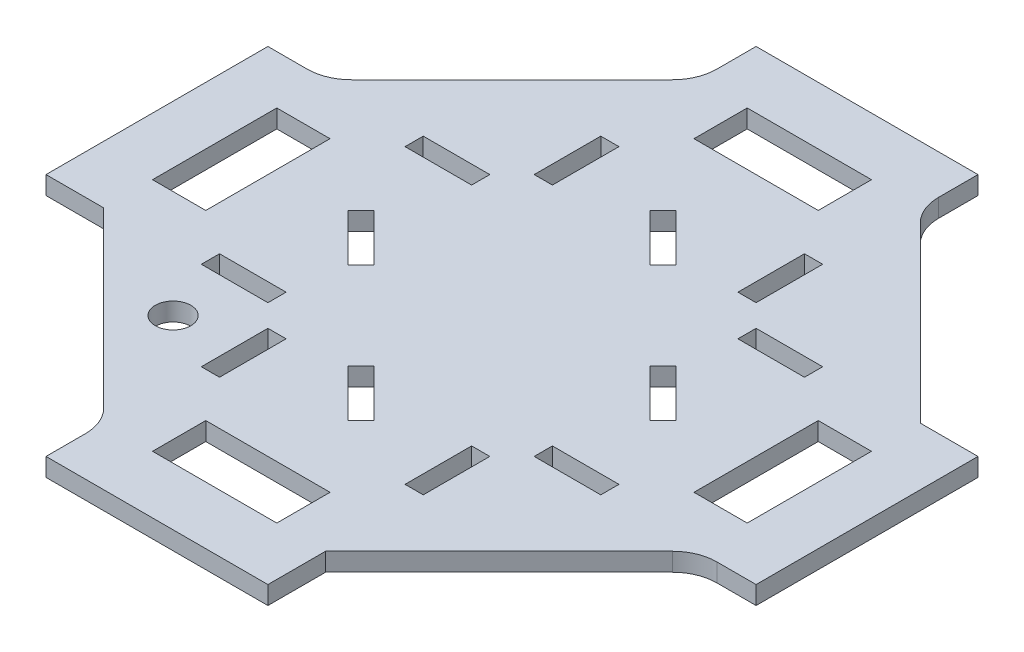
SolidWorks part; units mm, degrees
material "Corrugated Paper"
ref_plane "Front Plane" through (0, 0, 0) normal (0, 0, 1) x (1, 0, 0)
ref_plane "Top Plane" through (0, 0, 0) normal (0, 1, 0) x (1, 0, 0)
ref_plane "Right Plane" through (0, 0, 0) normal (1, 0, 0) x (0, 0, -1)
sketch "Sketch1" plane through (0, 0, 0) normal (0, 1, 0) x (1, 0, 0)
  line L0 (-20.9, 30) -> (-25, 30)
  line L1 (-55, -55) -> (55, -55) construction
  line L2 (-55, -55) -> (-55, 55) construction
  line L3 (-55, 55) -> (55, 55) construction
  line L4 (55, -55) -> (55, 55) construction
  line L5 (-55, -55) -> (55, 55) construction
  line L6 (-55, 55) -> (55, -55) construction
  line L7 (-30, 30) -> (30, 30) construction
  line L8 (-30, 30) -> (-30, -30) construction
  line L9 (-30, -30) -> (30, -30) construction
  line L10 (30, 30) -> (30, -30) construction
  line L11 (-30, 20.9) -> (-45, 20.9)
  line L12 (-30, 20.9) -> (-30, 25)
  line L13 (-30, 25) -> (-45, 25)
  line L14 (-45, 20.9) -> (-45, 25)
  line L15 (-25, 30) -> (-25, 45)
  line L16 (-20.9, 45) -> (-25, 45)
  line L17 (-20.9, 30) -> (-20.9, 45)
  line L18 (30, -20.9) -> (30, -25)
  line L19 (45, -20.9) -> (45, -25)
  line L20 (30, -25) -> (45, -25)
  line L21 (30, -20.9) -> (45, -20.9)
  line L22 (20.9, -30) -> (25, -30)
  line L23 (25, -30) -> (25, -45)
  line L24 (20.9, -45) -> (25, -45)
  line L25 (20.9, -30) -> (20.9, -45)
  line L26 (0, -55) -> (0, 55) construction
  line L27 (55, 0) -> (-55, 0) construction
  line L28 (45, 20.9) -> (45, 25)
  line L29 (30, 25) -> (45, 25)
  line L30 (30, 20.9) -> (30, 25)
  line L31 (30, 20.9) -> (45, 20.9)
  line L32 (-30, -20.9) -> (-30, -25)
  line L33 (-45, -20.9) -> (-45, -25)
  line L34 (-30, -25) -> (-45, -25)
  line L35 (-30, -20.9) -> (-45, -20.9)
  line L36 (20.9, 45) -> (25, 45)
  line L37 (25, 30) -> (25, 45)
  line L38 (20.9, 30) -> (25, 30)
  line L39 (20.9, 30) -> (20.9, 45)
  line L40 (-20.9, -30) -> (-25, -30)
  line L41 (-20.9, -45) -> (-25, -45)
  line L42 (-20.9, -30) -> (-20.9, -45)
  line L43 (-25, -30) -> (-25, -45)
  line L44 (-25, 67) -> (-67, 25)
  line L45 (-67, 25) -> (-80, 25)
  line L46 (-25, -67) -> (-67, -25)
  line L47 (-67, -25) -> (-80, -25)
  line L48 (-80, 25) -> (-80, -25)
  line L49 (25, -67) -> (67, -25)
  line L50 (-36.0624, 4.9497) -> (-25.4558, -5.6569)
  line L51 (67, 25) -> (80, 25)
  line L52 (80, 25) -> (80, -25)
  line L53 (67, -25) -> (80, -25)
  line L54 (-25.4558, -5.6569) -> (-28.355, -8.556)
  line L55 (-28.355, -8.556) -> (-38.9616, 2.0506)
  line L56 (25, -67) -> (25, -80)
  line L57 (25, -80) -> (-25, -80)
  line L58 (-25, -67) -> (-25, -80)
  line L59 (-38.9616, 2.0506) -> (-36.0624, 4.9497)
  line L60 (-25, 67) -> (-25, 80)
  line L61 (25, 80) -> (-25, 80)
  line L62 (25, 67) -> (25, 80)
  line L63 (-8.556, -28.355) -> (2.0506, -38.9616)
  line L92 (-67, -14) -> (-67, -25) construction
  line L93 (-67, -14) -> (-55, -14)
  line L94 (-67, -14) -> (-67, 14)
  line L95 (-67, 14) -> (-55, 14)
  line L96 (-55, -14) -> (-55, 14)
  line L97 (-67, 14) -> (-67, 25) construction
  line L98 (67, -14) -> (67, 14)
  line L99 (67, 14) -> (55, 14)
  line L100 (55, -14) -> (55, 14)
  line L101 (67, -14) -> (55, -14)
  line L102 (14, 67) -> (-14, 67)
  line L103 (14, 67) -> (14, 55)
  line L104 (14, 55) -> (-14, 55)
  line L105 (-14, 67) -> (-14, 55)
  line L106 (-14, -67) -> (-14, -55)
  line L107 (14, -67) -> (-14, -67)
  line L108 (14, -67) -> (14, -55)
  line L109 (14, -55) -> (-14, -55)
  line L110 (25, 67) -> (67, 25)
  line L111 (2.0506, -38.9616) -> (4.9497, -36.0624)
  line L112 (4.9497, -36.0624) -> (-5.6569, -25.4558)
  line L113 (-5.6569, -25.4558) -> (-8.556, -28.355)
  line L114 (38.9616, -2.0506) -> (36.0624, -4.9497)
  line L115 (28.355, 8.556) -> (38.9616, -2.0506)
  line L116 (36.0624, -4.9497) -> (25.4558, 5.6569)
  line L117 (25.4558, 5.6569) -> (28.355, 8.556)
  line L118 (8.556, 28.355) -> (-2.0506, 38.9616)
  line L119 (-2.0506, 38.9616) -> (-4.9497, 36.0624)
  line L120 (-4.9497, 36.0624) -> (5.6569, 25.4558)
  line L121 (5.6569, 25.4558) -> (8.556, 28.355)
  circle A0 centre (-38.1838, -38.1838) radius 4
  point P0 (0, 0)
  dimension "D9" = 8
  dimension "D11" = 54
  dimension "D2" = 110
  dimension "D3" = 30
  dimension "D4" = 15
  dimension "D5" = 4.1
  dimension "D6" = 50
  dimension "D7" = 50
  dimension "D8" = 80
  dimension "D10" = 12
  dimension "D13" = 28
  dimension "D14" = 15
  dimension "D15" = 4.1
  dimension "D16" = 44
  dimension "D17" = 14
extrude "Boss-Extrude1" add sketch "Sketch1" along normal blind 4.1
fillet "Fillet4" radius 10 5 edges at (-67, 2.05, -25) (25, 2.05, -67) (67, 2.05, 25) (-25, 2.05, 67) (-25, 2.05, -67)
